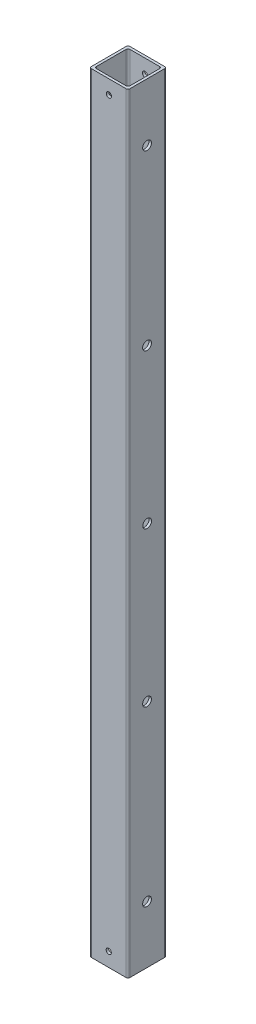
SolidWorks part; units mm, degrees
ref_plane "Front Plane" through (0, 0, 0) normal (0, 0, 1) x (1, 0, 0)
ref_plane "Top Plane" through (0, 0, 0) normal (0, 1, 0) x (1, 0, 0)
ref_plane "Right Plane" through (0, 0, 0) normal (1, 0, 0) x (0, 0, -1)
sketch "Sketch1" plane through (0, 0, 0) normal (0, 1, 0) x (1, 0, 0)
  line L0 (11.049, -11.049) -> (11.049, 11.049)
  line L1 (-12.7, -12.7) -> (12.7, -12.7)
  line L2 (-12.7, -12.7) -> (-12.7, 12.7)
  line L3 (-12.7, 12.7) -> (12.7, 12.7)
  line L4 (12.7, -12.7) -> (12.7, 12.7)
  line L5 (-12.7, -12.7) -> (12.7, 12.7) construction
  line L6 (-12.7, 12.7) -> (12.7, -12.7) construction
  line L7 (-11.049, 11.049) -> (11.049, 11.049)
  line L8 (-11.049, -11.049) -> (-11.049, 11.049)
  line L9 (-11.049, -11.049) -> (11.049, -11.049)
  point P0 (0, 0)
  dimension "D1" = 25.4
  dimension "D2" = 1.651
extrude "Boss-Extrude1" add sketch "Sketch1" along normal blind 508
fillet "Fillet1" radius 1.27 8 edges at (-12.7, 254, 12.7) (-12.7, 254, -12.7) (12.7, 254, -12.7) (12.7, 254, 12.7) (-11.049, 254, -11.049) (11.049, 254, 11.049) (11.049, 254, -11.049) (-11.049, 254, 11.049)
hole_wizard "#1 (0.228) Diameter Hole2" positions "Sketch4" profile "Sketch5" hole size "#1" standard "ANSI Inch" end condition through all
sketch "Sketch4" plane through (-12.7, 0, 0) normal (-1, 0, 0) x (0, 0, 1)
  point P8 (0.1524, 469.9)
  point P11 (0.1524, 355.6)
  point P14 (0.0762, 253.8476)
  point P17 (0.1524, 152.0952)
  point P20 (0.1524, 37.7952)
sketch "Sketch5" plane through (-12.7, 469.9, 0.1524) normal (0, 1, 0) x (0, 0, 1)
  line L0 (0, 0) -> (0, 25.4)
  line L1 (0, 25.4) -> (2.8956, 25.4)
  line L2 (2.8956, 25.4) -> (2.8956, 0)
  line L5 (2.8956, 0) -> (0, 0)
  line L11 (0, -6.35) -> (0, 107.95) construction
  dimension "Thru Hole Dia." = 5.7912
  dimension "Thru Hole Depth" = 25.4
hole_wizard "#8-32 Tapped Hole1" positions "Sketch6" profile "Sketch8" tap size "#8-32" standard "ANSI Inch" end condition through all
sketch "Sketch6" plane through (0, 0, 12.7) normal (0, 0, 1) x (1, 0, 0)
  line L1 (-11.43, 0) -> (11.43, 0) construction
  line L2 (-11.43, 508) -> (11.43, 508) construction
  point P5 (0, 9.271)
  point P15 (0.1031, 498.729)
  dimension "D1" = 9.271
  dimension "D2" = 9.271
sketch "Sketch8" plane through (0, 9.271, 12.7) normal (1, 0, 0) x (0, -1, 0)
  line L0 (0, 0) -> (0, 25.4)
  line L1 (0, 25.4) -> (1.7272, 25.4)
  line L2 (1.7272, 25.4) -> (1.7272, 0)
  line L5 (1.7272, 0) -> (0, 0)
  line L11 (0, -6.35) -> (0, 107.95) construction
  dimension "Thru Tap Drill Dia." = 3.4544
  dimension "Thru Tap Drill Depth" = 25.4
cosmetic thread "Hole Thread1" parameters "D2"=4.1656
cosmetic thread "Hole Thread2" parameters "D2"=4.1656
ref_plane "Plane1" through (-11.43, 508, 12.7) normal (1, 0, 0) x (0, 0, -1)
